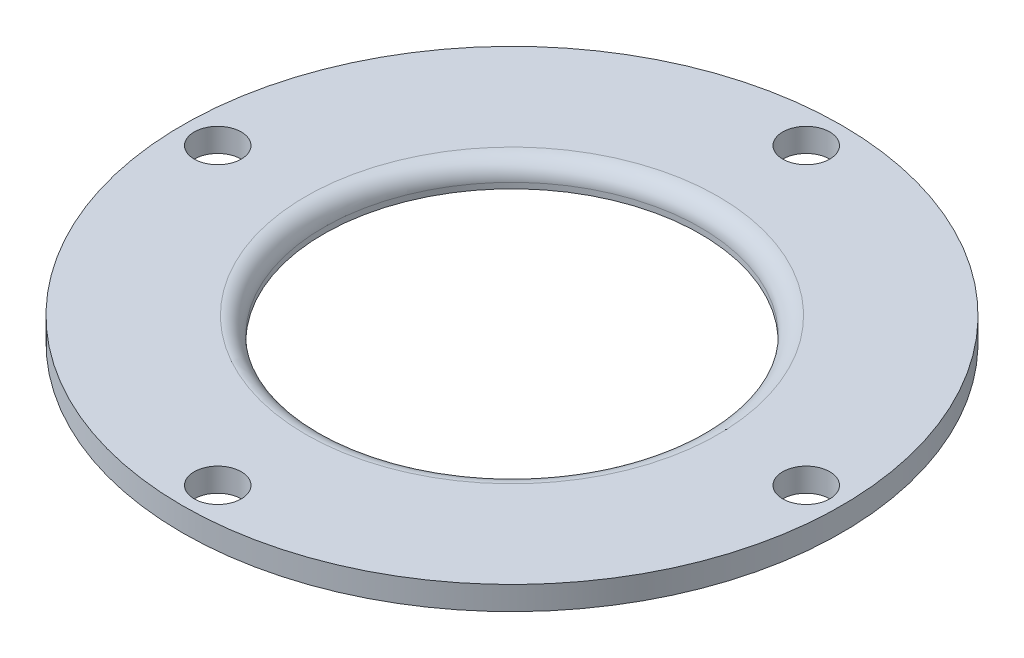
SolidWorks part; units mm, degrees
ref_plane "Front Plane" through (0, 0, 0) normal (0, 0, 1) x (1, 0, 0)
ref_plane "Top Plane" through (0, 0, 0) normal (0, 1, 0) x (1, 0, 0)
ref_plane "Right Plane" through (0, 0, 0) normal (1, 0, 0) x (0, 0, -1)
sketch "Sketch1" plane through (0, 0, 0) normal (0, 1, 0) x (1, 0, 0)
  circle A0 centre (0, 0) radius 88.9
  dimension "D1" = 177.8
extrude "Boss-Extrude1" add sketch "Sketch1" along normal blind 6.35
sketch "Sketch2" plane through (0, 6.35, 0) normal (0, 1, 0) x (1, 0, 0)
  circle A0 centre (0, 0) radius 50.8
  dimension "D1" = 101.6
extrude "Cut-Extrude1" cut sketch "Sketch2" against normal through all
fillet "Fillet2" radius 4.826 1 edges at (0, 6.35, 50.8)
sketch "Sketch3" plane through (0, 0, 0) normal (0, -1, 0) x (1, 0, 0)
  circle A1 centre (0, -79.375) radius 6.35
  circle A2 centre (79.375, 0) radius 6.35
  circle A3 centre (-79.375, 0) radius 6.35
  circle A4 centre (0, 79.375) radius 6.35
  point P10 (0, 0)
  dimension "D1" = 4
  dimension "D2" = 12.7
extrude "Cut-Extrude2" cut sketch "Sketch3" against normal through all
